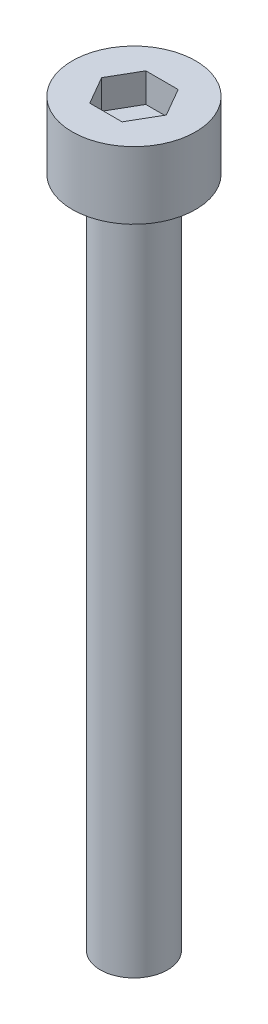
SolidWorks part; units mm, degrees
material "AISI 304"
ref_plane "前视基准面" through (0, 0, 0) normal (0, 0, 1) x (1, 0, 0)
ref_plane "上视基准面" through (0, 0, 0) normal (0, 1, 0) x (1, 0, 0)
ref_plane "右视基准面" through (0, 0, 0) normal (1, 0, 0) x (0, 0, -1)
sketch "草图1" plane through (0, 0, 0) normal (0, 1, 0) x (1, 0, 0)
  circle A0 centre (0, 0) radius 2.75
  dimension "D1" = 5.5
extrude "杯头" add sketch "草图1" along normal blind 3
sketch "草图2" plane through (0, 3, 0) normal (0, 1, 0) x (1, 0, 0)
  line L1 (1.4434, 0) -> (0.7217, 1.25)
  line L2 (0.7217, 1.25) -> (-0.7217, 1.25)
  line L3 (-0.7217, 1.25) -> (-1.4434, 0)
  line L4 (-1.4434, 0) -> (-0.7217, -1.25)
  line L5 (-0.7217, -1.25) -> (0.7217, -1.25)
  line L6 (0.7217, -1.25) -> (1.4434, 0)
  circle A0 centre (0, 0) radius 1.25 construction
  dimension "D1" = 2.5
extrude "内六角口" cut sketch "草图2" against normal blind 1.3
sketch "草图3" plane through (0, 0, 0) normal (0, -1, 0) x (1, 0, 0)
  circle A0 centre (0, 0) radius 1.5
  dimension "D1" = 3
extrude "螺纹长" add sketch "草图3" along normal blind 30
